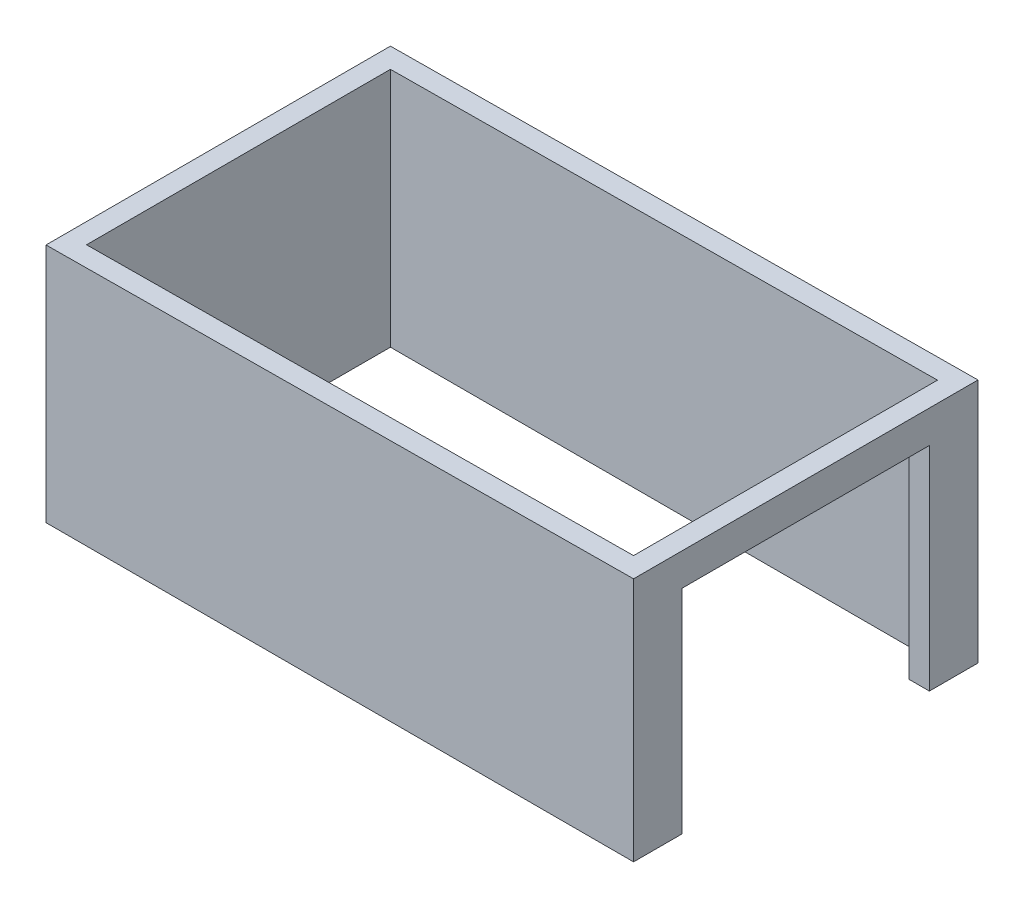
SolidWorks part; units mm, degrees
ref_plane "Спереди" through (0, 0, 0) normal (0, 0, 1) x (1, 0, 0)
ref_plane "Сверху" through (0, 0, 0) normal (0, 1, 0) x (1, 0, 0)
ref_plane "Справа" through (0, 0, 0) normal (1, 0, 0) x (0, 0, -1)
sketch "Эскиз1" plane through (0, 0, 0) normal (0, 1, 0) x (1, 0, 0)
  line L1 (0, 0) -> (5400, 0)
  line L2 (0, 0) -> (0, 3000)
  line L3 (0, 3000) -> (5400, 3000)
  line L4 (5400, 0) -> (5400, 3000)
extrude "Вытянуть-Тонкостенный1" add sketch "Эскиз1" along normal blind 2420 thin
sketch "Эскиз2" plane through (5600, 0, 0) normal (1, 0, 0) x (0, 0, -1)
  line L0 (-200, 0) -> (3200, 0) construction
  line L1 (280, 0) -> (2720, 0)
  line L2 (280, 0) -> (280, 2100)
  line L3 (280, 2100) -> (2720, 2100)
  line L4 (2720, 0) -> (2720, 2100)
extrude "Вырез-Вытянуть1" cut sketch "Эскиз2" against normal up to next
sketch "Эскиз3" plane through (0, 0, -3200) normal (0, 0, -1) x (-1, 0, 0)
  line L0 (-5600, 2420) -> (200, 2420)
  line L1 (200, 2420) -> (200, 2374)
  line L2 (200, 2420) -> (200, 0) construction
  line L3 (200, 2374) -> (-5600, 2420)
extrude "Вырез-Вытянуть2" cut sketch "Эскиз3" against normal through all
